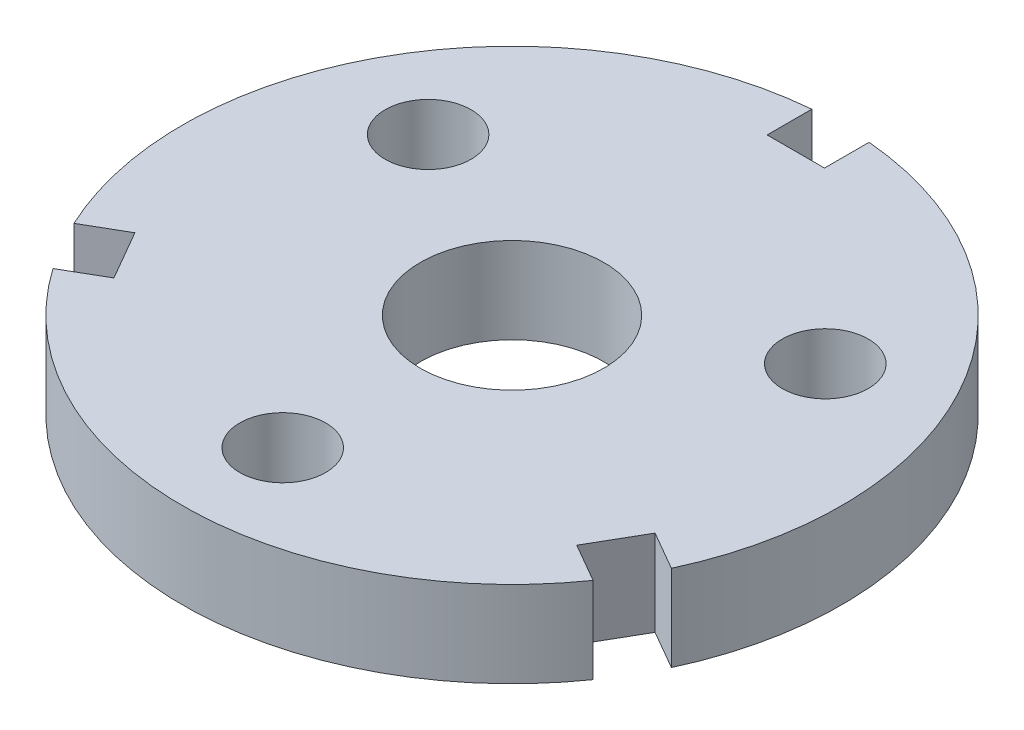
SolidWorks part; units mm, degrees
ref_plane "Front Plane" through (0, 0, 0) normal (0, 0, 1) x (1, 0, 0)
ref_plane "Top Plane" through (0, 0, 0) normal (0, 1, 0) x (1, 0, 0)
ref_plane "Right Plane" through (0, 0, 0) normal (1, 0, 0) x (0, 0, -1)
sketch "Sketch1" plane through (0, 0, 0) normal (0, 1, 0) x (1, 0, 0)
  line L0 (-5, 57.2822) -> (-5, 49.5)
  line L2 (-5, 49.5) -> (5, 49.5)
  line L3 (5, 49.5) -> (5, 57.2822)
  line L4 (52.1078, -24.311) -> (45.3683, -20.4199)
  line L5 (45.3683, -20.4199) -> (40.3683, -29.0801)
  line L6 (40.3683, -29.0801) -> (47.1078, -32.9712)
  line L7 (-47.1078, -32.9712) -> (-40.3683, -29.0801)
  line L8 (-40.3683, -29.0801) -> (-45.3683, -20.4199)
  line L9 (-45.3683, -20.4199) -> (-52.1078, -24.311)
  circle A0 centre (0, 0) radius 16
  arc A2 (-5, 57.2822) -> (-52.1078, -24.311) centre (0, 0) ccw
  circle A3 centre (34.641, 20) radius 7.5
  circle A4 centre (0, -40) radius 7.5
  circle A5 centre (-34.641, 20) radius 7.5
  arc A6 (-47.1078, -32.9712) -> (47.1078, -32.9712) centre (0, 0) ccw
  arc A7 (52.1078, -24.311) -> (5, 57.2822) centre (0, 0) ccw
  point P16 (0, 0)
  point P17 (0, 57.5)
  point P30 (0, 0)
  dimension "D1" = 32
  dimension "D3" = 115
  dimension "D5" = 15
  dimension "D4" = 3
  dimension "D6" = 8
  dimension "D7" = 5
  dimension "D8" = 5
  dimension "D9" = 3
extrude "Boss-Extrude1" add sketch "Sketch1" along normal blind 15
